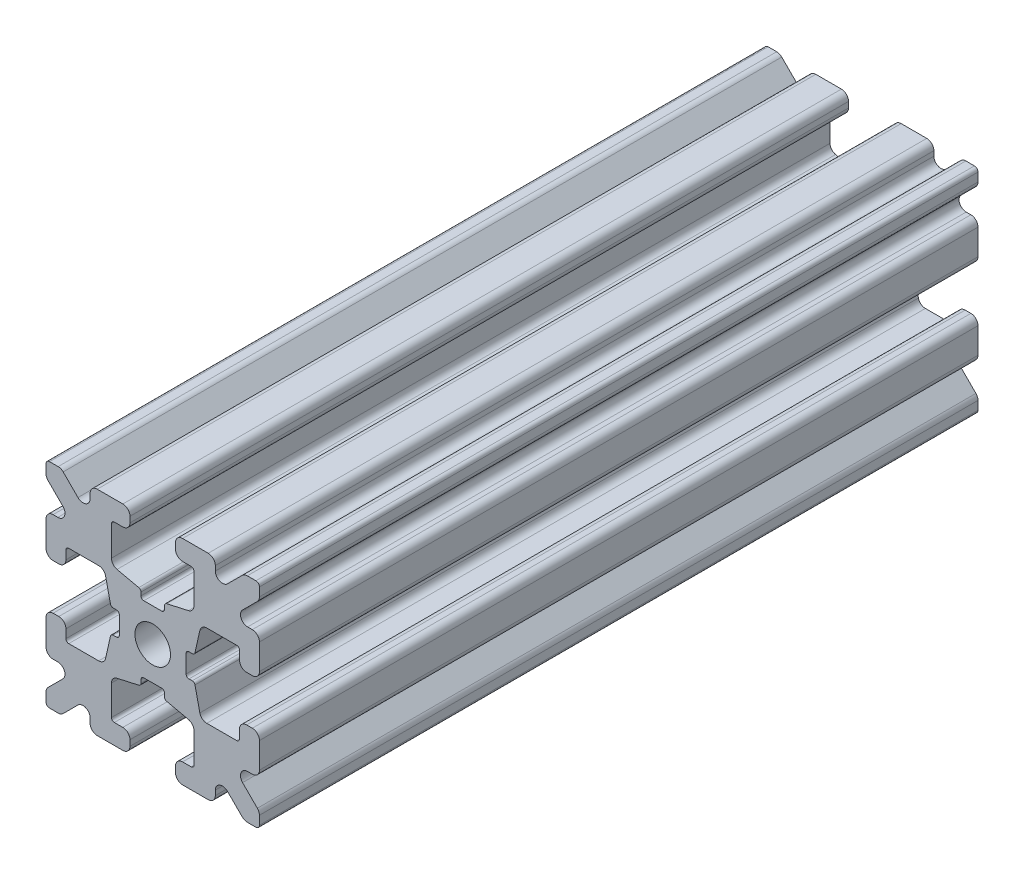
SolidWorks part; units mm, degrees
ref_plane "Front Plane" through (0, 0, 0) normal (0, 0, 1) x (1, 0, 0)
ref_plane "Top Plane" through (0, 0, 0) normal (0, 1, 0) x (1, 0, 0)
ref_plane "Right Plane" through (0, 0, 0) normal (1, 0, 0) x (0, 0, -1)
sketch "Sketch1" plane through (0, 0, 0) normal (0, 0, 1) x (1, 0, 0)
  line L1 (-7.5, -7.5) -> (7.5, -7.5)
  line L2 (-7.5, -7.5) -> (-7.5, 7.5)
  line L3 (-7.5, 7.5) -> (7.5, 7.5)
  line L4 (7.5, -7.5) -> (7.5, 7.5)
  line L5 (-7.5, -7.5) -> (7.5, 7.5) construction
  line L6 (-7.5, 7.5) -> (7.5, -7.5) construction
  circle A0 centre (0, 0) radius 1.25
  point P0 (0, 0)
  dimension "D2" = 2.5
  dimension "D1" = 15
extrude "Boss-Extrude1" add sketch "Sketch1" along normal mid plane 50.5
fillet "Fillet1" radius 0.25 4 edges at (7.5, -7.5, 0) (-7.5, -7.5, 0) (7.5, 7.5, 0) (-7.5, 7.5, 0)
sketch "Sketch2" plane through (0, 0, 25.25) normal (0, 0, 1) x (1, 0, 0)
  line L0 (-7.5, 7.25) -> (-7.5, -7.25) construction
  line L1 (-7.5, 1.6) -> (-6.1, 1.6)
  line L2 (-7.5, 1.6) -> (-7.5, -1.6)
  line L3 (-7.5, -1.6) -> (-6.1, -1.6)
  line L4 (-6.1, 1.6) -> (-6.1, 2.9)
  line L5 (0, 0) -> (-12.1036, 0) construction
  line L6 (-6.1, -2.9) -> (-3.4, -2.9)
  line L7 (0, 0) -> (-7.25, 7.25) construction
  line L8 (-6.1, 2.9) -> (-3.4, 2.9)
  line L9 (-3.4, -2.9) -> (-3.4, 2.9)
  line L10 (55, 0) -> (-55, 0) construction
  line L11 (-6.1, -2.9) -> (-6.1, -1.6)
  line L12 (2.9, 6.1) -> (1.6, 6.1)
  line L13 (2.9, 3.4) -> (-2.9, 3.4)
  line L14 (-2.9, 6.1) -> (-2.9, 3.4)
  line L15 (2.9, 6.1) -> (2.9, 3.4)
  line L16 (-1.6, 6.1) -> (-2.9, 6.1)
  line L17 (1.6, 7.5) -> (1.6, 6.1)
  line L18 (-1.6, 7.5) -> (1.6, 7.5)
  line L19 (-1.6, 7.5) -> (-1.6, 6.1)
  line L20 (-1.6, -7.5) -> (-1.6, -6.1)
  line L21 (-1.6, -7.5) -> (1.6, -7.5)
  line L22 (1.6, -7.5) -> (1.6, -6.1)
  line L23 (-1.6, -6.1) -> (-2.9, -6.1)
  line L24 (2.9, -6.1) -> (2.9, -3.4)
  line L25 (-2.9, -6.1) -> (-2.9, -3.4)
  line L26 (2.9, -3.4) -> (-2.9, -3.4)
  line L27 (2.9, -6.1) -> (1.6, -6.1)
  line L28 (6.1, -2.9) -> (6.1, -1.6)
  line L29 (3.4, -2.9) -> (3.4, 2.9)
  line L30 (6.1, 2.9) -> (3.4, 2.9)
  line L31 (6.1, -2.9) -> (3.4, -2.9)
  line L32 (6.1, 1.6) -> (6.1, 2.9)
  line L33 (7.5, -1.6) -> (6.1, -1.6)
  line L34 (7.5, 1.6) -> (7.5, -1.6)
  line L35 (7.5, 1.6) -> (6.1, 1.6)
  dimension "D1" = 3.2
  dimension "D2" = 5.8
  dimension "D3" = 1.4
  dimension "D4" = 2.7
extrude "Cut-Extrude1" cut sketch "Sketch2" against normal through all
sketch "Sketch4" plane through (0, 0, 25.25) normal (0, 0, 1) x (1, 0, 0)
  line L0 (-3.4, 2.9) -> (-2.75, 0)
  line L1 (55, 0) -> (-55, 0) construction
  line L2 (-2.75, 0) -> (-3.4, -2.9)
  line L3 (-3.4, -2.9) -> (-3.4, 2.9) construction
  line L4 (-3.4, 2.9) -> (-3.4, -2.9)
  line L5 (-2.9, 3.4) -> (0, 2.75)
  line L6 (0, 2.75) -> (2.9, 3.4)
  line L7 (2.9, 3.4) -> (-2.9, 3.4)
  line L8 (3.4, 2.9) -> (2.75, 0)
  line L9 (2.75, 0) -> (3.4, -2.9)
  line L10 (3.4, -2.9) -> (3.4, 2.9)
  line L11 (-2.9, -3.4) -> (0, -2.75)
  line L12 (0, -2.75) -> (2.9, -3.4)
  line L13 (2.9, -3.4) -> (-2.9, -3.4)
  circle A2 centre (0, 0) radius 2.75
  circle A3 centre (0, 0) radius 2.75 construction
  dimension "D1" = 1.5
extrude "Cut-Extrude3" cut sketch "Sketch4" against normal through all
fillet "Fillet3" radius 0.5 16 edges at (-6.1, -1.6, 0) (-7.5, -1.6, 0) (-6.1, 1.6, 0) (-7.5, 1.6, 0) (-1.6, -7.5, 0) (-1.6, -6.1, 0) (1.6, -7.5, 0) (1.6, -6.1, 0) (6.1, -1.6, 0) (7.5, -1.6, 0) (7.5, 1.6, 0) (6.1, 1.6, 0) (1.6, 7.5, 0) (1.6, 6.1, 0) (-1.6, 7.5, 0) (-1.6, 6.1, 0)
fillet "Fillet4" radius 0.5 8 edges at (-3.4, 2.9, 0) (-3.4, -2.9, 0) (2.9, -3.4, 0) (-2.9, -3.4, 0) (3.4, -2.9, 0) (3.4, 2.9, 0) (-2.9, 3.4, 0) (2.9, 3.4, 0)
fillet "Fillet5" radius 3 4 edges at (0, -2.75, 0) (2.75, 0, 0) (-2.75, 0, 0) (0, 2.75, 0)
fillet "Fillet6" radius 0.2 8 edges at (-2.9, -6.1, 0) (2.9, -6.1, 0) (6.1, -2.9, 0) (6.1, 2.9, 0) (2.9, 6.1, 0) (-2.9, 6.1, 0) (-6.1, -2.9, 0) (-6.1, 2.9, 0)
sketch "Sketch5" plane through (0, 0, 25.25) normal (0, 0, 1) x (1, 0, 0)
  line L0 (0, 0) -> (-7.25, 7.25) construction
  line L1 (-7.5, 6.4393) -> (-5.4607, 4.4)
  line L2 (-6.4393, 7.5) -> (-4.4, 5.4607)
  line L3 (-7.5, 4.4) -> (-5.4607, 4.4)
  line L4 (-3.8003, 2.9) -> (-5.9, 2.9) construction
  line L5 (0, 0) -> (-12.1819, 0) construction
  line L6 (-4.4, 7.5) -> (-4.4, 5.4607)
  line L7 (-2.9, 5.9) -> (-2.9, 3.8003) construction
  line L8 (-7.5, 6.4393) -> (-7.5, 4.4)
  line L9 (-7.5, 7.25) -> (-7.5, 2.1) construction
  line L10 (2.1, -7.5) -> (7.25, -7.5) construction
  line L11 (7.5, -7.25) -> (7.5, -2.1) construction
  line L12 (7.25, 7.5) -> (2.1, 7.5) construction
  line L13 (-2.1, 7.5) -> (-7.25, 7.5) construction
  line L14 (-4.4, 7.5) -> (-6.4393, 7.5)
  line L16 (55, 0) -> (-55, 0) construction
  line L17 (0, 0) -> (0, 10.993) construction
  line L18 (0, -54.6431) -> (0, 54.6431) construction
  line L20 (4.4, 7.5) -> (6.4393, 7.5)
  line L22 (7.5, 6.4393) -> (7.5, 4.4)
  line L23 (4.4, 7.5) -> (4.4, 5.4607)
  line L24 (7.5, 4.4) -> (5.4607, 4.4)
  line L25 (6.4393, 7.5) -> (4.4, 5.4607)
  line L26 (7.5, 6.4393) -> (5.4607, 4.4)
  line L27 (7.5, -6.4393) -> (5.4607, -4.4)
  line L28 (6.4393, -7.5) -> (4.4, -5.4607)
  line L29 (7.5, -4.4) -> (5.4607, -4.4)
  line L30 (4.4, -7.5) -> (4.4, -5.4607)
  line L31 (7.5, -6.4393) -> (7.5, -4.4)
  line L33 (4.4, -7.5) -> (6.4393, -7.5)
  line L36 (-4.4, -7.5) -> (-6.4393, -7.5)
  line L38 (-7.5, -6.4393) -> (-7.5, -4.4)
  line L39 (-4.4, -7.5) -> (-4.4, -5.4607)
  line L40 (-7.5, -4.4) -> (-5.4607, -4.4)
  line L41 (-6.4393, -7.5) -> (-4.4, -5.4607)
  line L42 (-7.5, -6.4393) -> (-5.4607, -4.4)
  dimension "D1" = 1.5
  dimension "D2" = 1.5
  dimension "D3" = 1.5
extrude "Cut-Extrude4" cut sketch "Sketch5" against normal through all
fillet "Fillet8" radius 0.5 24 edges at (-5.4607, 4.4, 0) (-7.5, 4.4, 0) (-5.4607, -4.4, 0) (-7.5, -4.4, 0) (-4.4, -7.5, 0) (-4.4, -5.4607, 0) (4.4, -7.5, 0) (4.4, -5.4607, 0) (5.4607, -4.4, 0) (7.5, -4.4, 0) (7.5, 4.4, 0) (5.4607, 4.4, 0) (4.4, 5.4607, 0) (4.4, 7.5, 0) (-4.4, 5.4607, 0) (-4.4, 7.5, 0) (-6.4393, 7.5, 0) (-7.5, 6.4393, 0) (6.4393, 7.5, 0) (7.5, 6.4393, 0) (6.4393, -7.5, 0) (7.5, -6.4393, 0) (-6.4393, -7.5, 0) (-7.5, -6.4393, 0)
sketch "Sketch6" plane through (0, 0, 25.25) normal (0, 0, 1) x (1, 0, 0)
  line L0 (0, 0) -> (0, 11.013) construction
  line L1 (0.6561, 2.8971) -> (2.1235, 2.8971) construction
  line L2 (0, -54.6431) -> (0, 54.6431) construction
  line L3 (0, 0) -> (7.25, 7.25) construction
  line L4 (7.5, 0.8255) -> (7.5, -0.8255)
  line L5 (2.3471, 0.8255) -> (7.5, 0.8255)
  line L6 (0, 0) -> (12.4016, 0) construction
  line L7 (0.8255, -7.5) -> (-0.8255, -7.5)
  line L8 (2.3471, -0.8255) -> (2.3471, 0.8255)
  line L9 (0.8255, -2.3471) -> (0.8255, -7.5)
  line L10 (7.5, -0.8255) -> (2.3471, -0.8255)
  line L11 (-7.5, -0.8255) -> (-2.3471, -0.8255)
  line L12 (-2.3471, -0.8255) -> (-2.3471, 0.8255)
  line L13 (-0.8255, -2.3471) -> (0.8255, -2.3471)
  line L14 (-0.8255, 7.5) -> (-0.8255, 2.3471)
  line L15 (-0.8255, 2.3471) -> (0.8255, 2.3471)
  line L16 (-0.8255, -7.5) -> (-0.8255, -2.3471)
  line L17 (0.8255, 2.3471) -> (0.8255, 7.5)
  line L18 (0.8255, 7.5) -> (-0.8255, 7.5)
  line L19 (3.9, 7.5) -> (2.1, 7.5) construction
  line L20 (-2.3471, 0.8255) -> (-7.5, 0.8255)
  line L21 (-7.5, 0.8255) -> (-7.5, -0.8255)
  point P5 (0, -2.5973)
  point P7 (0, 2.5973)
  dimension "D3" = 0.55
  dimension "D1" = 1.651
extrude "Cut-Extrude5" cut sketch "Sketch6" against normal through all
fillet "Fillet10" radius 0.2 16 edges at (-2.935, 0.8255, 0) (-2.935, -0.8255, 0) (2.935, -0.8255, 0) (2.935, 0.8255, 0) (0.8255, 2.935, 0) (-0.8255, 2.935, 0) (-2.3471, 0.8255, 0) (-2.3471, -0.8255, 0) (0.8255, 2.3471, 0) (-0.8255, 2.3471, 0) (2.3471, 0.8255, 0) (2.3471, -0.8255, 0) (0.8255, -2.935, 0) (0.8255, -2.3471, 0) (-0.8255, -2.3471, 0) (-0.8255, -2.935, 0)
